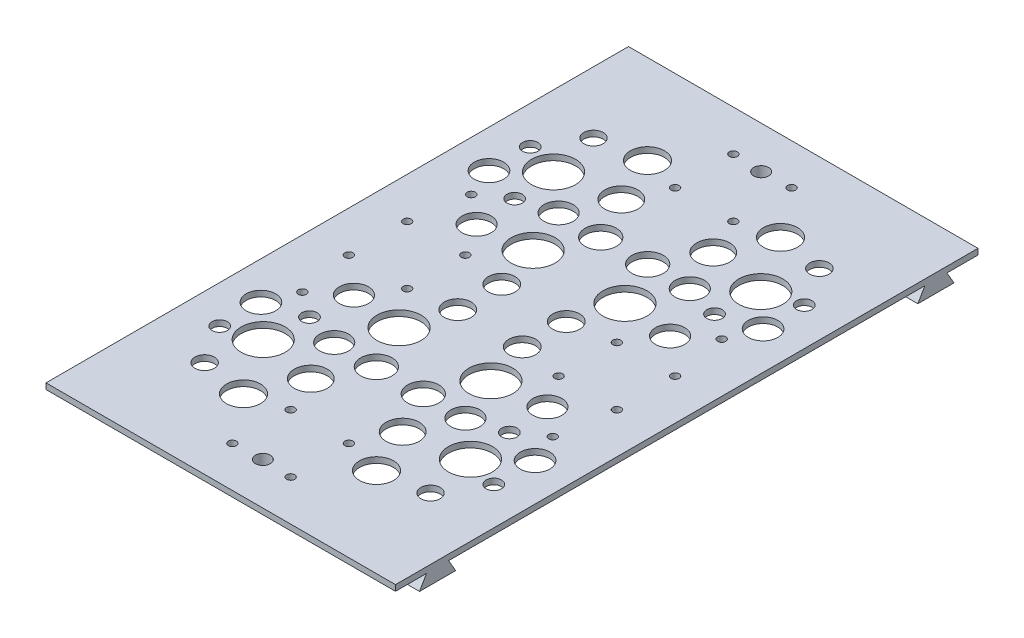
SolidWorks part; units mm, degrees
ref_plane "Front Plane" through (0, 0, 0) normal (0, 0, 1) x (1, 0, 0)
ref_plane "Top Plane" through (0, 0, 0) normal (0, 1, 0) x (1, 0, 0)
ref_plane "Right Plane" through (0, 0, 0) normal (1, 0, 0) x (0, 0, -1)
sketch "JetsonMountingHoles" plane through (0, 0, 0) normal (0, 1, 0) x (1, 0, 0)
  line L0 (0, -1000) -> (0, 49000) construction
  line L1 (-1000, 0) -> (49000, 0) construction
  circle A0 centre (-43, 29) radius 1.38
  circle A1 centre (43, 29) radius 1.38
  circle A2 centre (-43, -29) radius 1.38
  circle A3 centre (43, -29) radius 1.38
  dimension "D1" = 2.76
  dimension "D2" = 2.76
  dimension "D3" = 2.76
  dimension "D4" = 2.76
  dimension "D5" = 86
  dimension "D6" = 58
sketch "BodyPerimeter" plane through (0, 0, 0) normal (0, 1, 0) x (1, 0, 0)
  line L0 (-60, -1000) -> (-60, 49000) construction
  line L2 (56.5019, -1000) -> (50056.5019, -1000) construction
  line L4 (-1000, 100) -> (49000, 100) construction
  line L6 (-1000, -100) -> (49000, -100) construction
  line L8 (60, -1000) -> (60, 49000) construction
  line L10 (0, -201000) -> (0, 249000) construction
  line L11 (-201000, 0) -> (249000, 0) construction
  dimension "D1" = 60
  dimension "D2" = 60
  dimension "D3" = 100
  dimension "D4" = 100
sketch "Sketch3" plane through (0, 0, 0) normal (0, 1, 0) x (1, 0, 0)
  line L0 (-60, 100) -> (60, 100)
  line L1 (-60, -201000) -> (-60, 249000) construction
  line L2 (-201000, 100) -> (249000, 100) construction
  line L3 (60, -201000) -> (60, 249000) construction
  line L4 (60, 100) -> (60, -100)
  line L5 (-201000, -100) -> (249000, -100) construction
  line L6 (60, -100) -> (-60, -100)
  line L7 (-60, -100) -> (-60, 100)
  circle A0 centre (-43, 29) radius 1.38
  circle A1 centre (43, 29) radius 1.38
  circle A2 centre (43, -29) radius 1.38
  circle A3 centre (-43, -29) radius 1.38
  circle A4 centre (-43, 29) radius 1.38 construction
  circle A5 centre (-43, -29) radius 1.38 construction
  circle A6 centre (43, -29) radius 1.38 construction
  circle A8 centre (43, 29) radius 1.38 construction
extrude "Boss-Extrude1" add sketch "Sketch3" along normal blind 2
sketch "Sketch4" plane through (-60, 0, 0) normal (-1, 0, 0) x (0, 0, 1)
  line L0 (-89.35, 0) -> (-91.7518, -4.16)
  line L1 (201000, 0) -> (-249000, 0) construction
  line L2 (-91.7518, -4.16) -> (-79.3482, -4.16)
  line L3 (-79.3482, -4.16) -> (-81.75, 0)
  line L4 (-81.75, 0) -> (-89.35, 0)
  line L5 (81.75, 0) -> (79.3482, -4.16)
  line L6 (79.3482, -4.16) -> (91.7518, -4.16)
  line L7 (91.7518, -4.16) -> (89.35, 0)
  line L8 (89.35, 0) -> (81.75, 0)
  line L9 (-100, 2) -> (-100, 0) construction
  line L10 (100, 2) -> (100, 0) construction
  dimension "D1" = 7.6
  dimension "D2" = 7.6
  dimension "D3" = 60
  dimension "D4" = 60
  dimension "D5" = 60
  dimension "D6" = 60
  dimension "D7" = 4.16
  dimension "D8" = 4.16
  dimension "D9" = 10.65
  dimension "D10" = 10.65
extrude "Boss-Extrude2" add sketch "Sketch4" against normal up to surface (120 mm away) up to face at (60, 1, 0)
sketch "Sketch5" plane through (0, 2, 0) normal (0, 1, 0) x (1, 0, 0)
  line L1 (-201000, -100) -> (249000, -100) construction
  line L2 (-60, -201000) -> (-60, 249000) construction
  line L3 (60, -201000) -> (60, 249000) construction
  line L4 (-201000, 100) -> (249000, 100) construction
  line L7 (-1000, 0) -> (49000, 0) construction
  line L9 (0, -1000) -> (0, 49000) construction
  circle A0 centre (-10, -86) radius 1.38
  circle A1 centre (10, -86) radius 1.38
  circle A2 centre (-46, 10) radius 1.38
  circle A3 centre (-46, -10) radius 1.38
  circle A4 centre (-26, 10) radius 1.38
  circle A5 centre (-26, -10) radius 1.38
  circle A6 centre (26, 10) radius 1.38
  circle A7 centre (26, -10) radius 1.38
  circle A8 centre (46, 10) radius 1.38
  circle A9 centre (46, -10) radius 1.38
  circle A10 centre (-10, -66) radius 1.38
  circle A11 centre (10, -66) radius 1.38
  circle A12 centre (-10, 86) radius 1.38
  circle A13 centre (10, 86) radius 1.38
  circle A14 centre (-10, 66) radius 1.38
  circle A15 centre (10, 66) radius 1.38
  dimension "D1" = 2.76
  dimension "D2" = 2.76
  dimension "D3" = 2.76
  dimension "D4" = 2.76
  dimension "D5" = 2.76
  dimension "D6" = 2.76
  dimension "D7" = 2.76
  dimension "D8" = 2.76
  dimension "D9" = 2.76
  dimension "D10" = 2.76
  dimension "D11" = 2.76
  dimension "D12" = 2.76
  dimension "D13" = 2.76
  dimension "D14" = 2.76
  dimension "D15" = 2.76
  dimension "D16" = 2.76
  dimension "D17" = 20
  dimension "D18" = 20
  dimension "D19" = 20
  dimension "D20" = 20
  dimension "D21" = 20
  dimension "D22" = 20
  dimension "D23" = 20
  dimension "D24" = 20
  dimension "D25" = 14
  dimension "D26" = 14
  dimension "D27" = 14
  dimension "D28" = 14
extrude "Cut-Extrude1" cut sketch "Sketch5" against normal through all
sketch "Sketch7" plane through (0, 2, 0) normal (0, 1, 0) x (1, 0, 0)
  circle A0 centre (-22.5211, -38.5218) radius 4.9987
  circle A1 centre (-35.5762, -49.8467) radius 7.5547
  circle A2 centre (-15.7703, -53.3071) radius 5.6939
  circle A3 centre (-38.7792, -66.7652) radius 3.3388
  circle A4 centre (-22.8357, -69.3506) radius 5.8431
  circle A5 centre (-15.7703, -23.0192) radius 7.5547
  circle A6 centre (-8.0505, -38.5218) radius 5.3801
  circle A7 centre (-11.0798, -7.5457) radius 4.5938
  circle A8 centre (-34.3178, -35.2188) radius 2.6367
  circle A9 centre (-33.2168, -21.0627) radius 4.9987
  circle A11 centre (-47.0583, -39.151) radius 5.0651
  circle A12 centre (-47.0583, -53.3071) radius 2.6367
extrude "Cut-Extrude2" cut sketch "Sketch7" against normal through all
mirror "Mirror1" about plane through (0, 0, 0) normal (0, 0, 1) of "Cut-Extrude2"
mirror "Mirror2" about plane through (0, 0, 0) normal (1, 0, 0) of "Cut-Extrude2", "Mirror1"
sketch "Sketch8" plane through (0, -4.16, 0) normal (0, -1, 0) x (1, 0, 0)
  line L0 (0, 201000) -> (0, -249000) construction
  line L1 (-1042.1999, 85.55) -> (48957.8001, 85.55) construction
  line L2 (60, 79.3482) -> (-60, 79.3482) construction
  line L3 (60, 91.7518) -> (-60, 91.7518) construction
  circle A0 centre (0, 85.55) radius 2.55
  point P10 (0, 0)
  dimension "D1" = 5.1
extrude "Cut-Extrude3" cut sketch "Sketch8" against normal through all
mirror "Mirror3" about plane through (0, 0, 0) normal (0, 0, 1) of "Cut-Extrude3"
equation "\"jetson_hole\"= 2.76"
equation "\"D2@JetsonMountingHoles\" = \"jetson_hole\""
equation "\"D1@JetsonMountingHoles\"=\"jetson_hole\""
equation "\"D3@JetsonMountingHoles\"=\"jetson_hole\""
equation "\"D4@JetsonMountingHoles\"=\"jetson_hole\""
equation "\"mounting_hole\"= 2.76"
equation "\"D2@Sketch5\"=\"mounting_hole\""
equation "\"D1@Sketch5\"=\"mounting_hole\""
equation "\"D3@Sketch5\"=\"mounting_hole\""
equation "\"D4@Sketch5\"=\"mounting_hole\""
equation "\"D5@Sketch5\"=\"mounting_hole\""
equation "\"D6@Sketch5\"=\"mounting_hole\""
equation "\"D7@Sketch5\"=\"mounting_hole\""
equation "\"D8@Sketch5\"=\"mounting_hole\""
equation "\"D9@Sketch5\"=\"mounting_hole\""
equation "\"D10@Sketch5\"=\"mounting_hole\""
equation "\"D11@Sketch5\"=\"mounting_hole\""
equation "\"D12@Sketch5\"=\"mounting_hole\""
equation "\"D13@Sketch5\"=\"mounting_hole\""
equation "\"D14@Sketch5\"=\"mounting_hole\""
equation "\"D15@Sketch5\"=\"mounting_hole\""
equation "\"D16@Sketch5\"=\"mounting_hole\""
